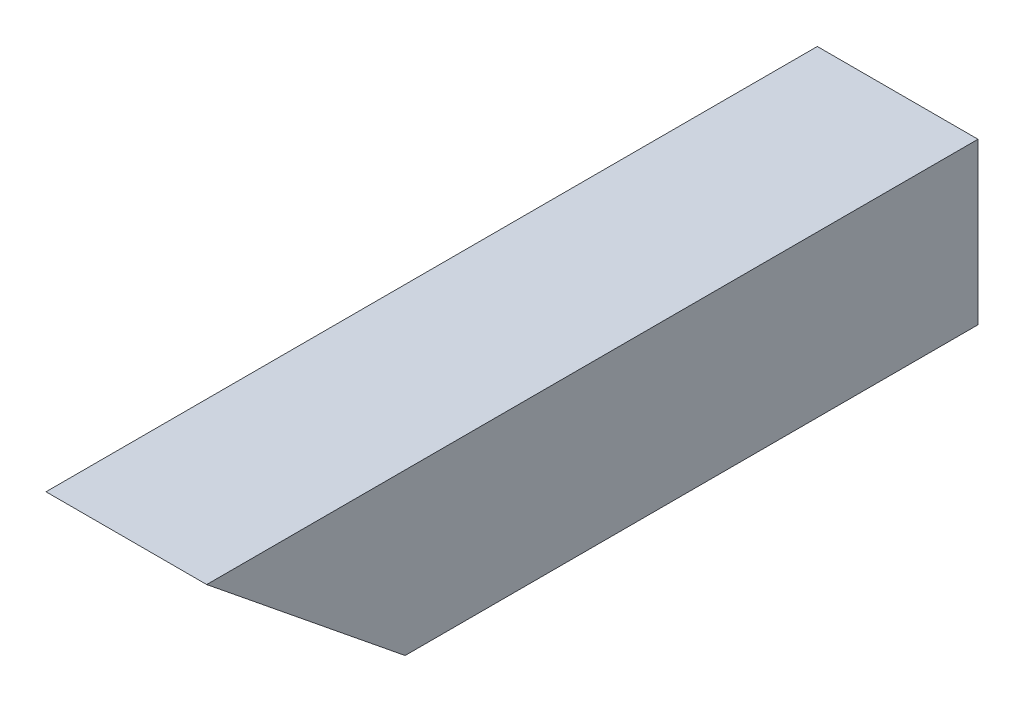
SolidWorks part; units mm, degrees
ref_plane "Front Plane" through (0, 0, 0) normal (0, 0, 1) x (1, 0, 0)
ref_plane "Top Plane" through (0, 0, 0) normal (0, 1, 0) x (1, 0, 0)
ref_plane "Right Plane" through (0, 0, 0) normal (1, 0, 0) x (0, 0, -1)
sketch "Sketch1" plane through (0, 0, 0) normal (0, 0, 1) x (1, 0, 0)
  line L5 (-12.827, 12.827) -> (12.827, 12.827)
  line L6 (-12.827, 12.827) -> (-12.827, -12.827)
  line L11 (-12.827, -12.827) -> (12.827, -12.827)
  line L12 (12.827, 12.827) -> (12.827, -12.827)
  line L13 (-12.827, 12.827) -> (12.827, -12.827) construction
  line L14 (-12.827, -12.827) -> (12.827, 12.827) construction
  line L15 (15.875, -15.875) -> (-15.875, -15.875)
  line L16 (15.875, -15.875) -> (15.875, 15.875)
  line L17 (15.875, 15.875) -> (-15.875, 15.875)
  line L18 (-15.875, -15.875) -> (-15.875, 15.875)
  line L19 (15.875, -15.875) -> (-15.875, 15.875) construction
  line L20 (15.875, 15.875) -> (-15.875, -15.875) construction
  point P0 (0, 0)
  point P6 (0, 0)
  dimension "D1" = 3.048
  dimension "D2" = 31.75
extrude "Boss-Extrude1" add sketch "Sketch1" along normal blind 152.4
sketch "Sketch2" plane through (0, 0, 0) normal (1, 0, 0) x (0, 0, -1)
  line L0 (-152.4, 15.875) -> (-113.192, -15.875)
  line L1 (-152.4, -15.875) -> (0, -15.875) construction
  line L2 (-113.192, -15.875) -> (-152.4, -15.875)
  line L3 (-152.4, -15.875) -> (-152.4, 15.875)
  line L6 (0, -15.875) -> (0, 15.875) construction
  dimension "D1" = 51
  dimension "D2" = 152.4
extrude "Cut-Extrude1" cut sketch "Sketch2" against normal through all both and the other way through all
